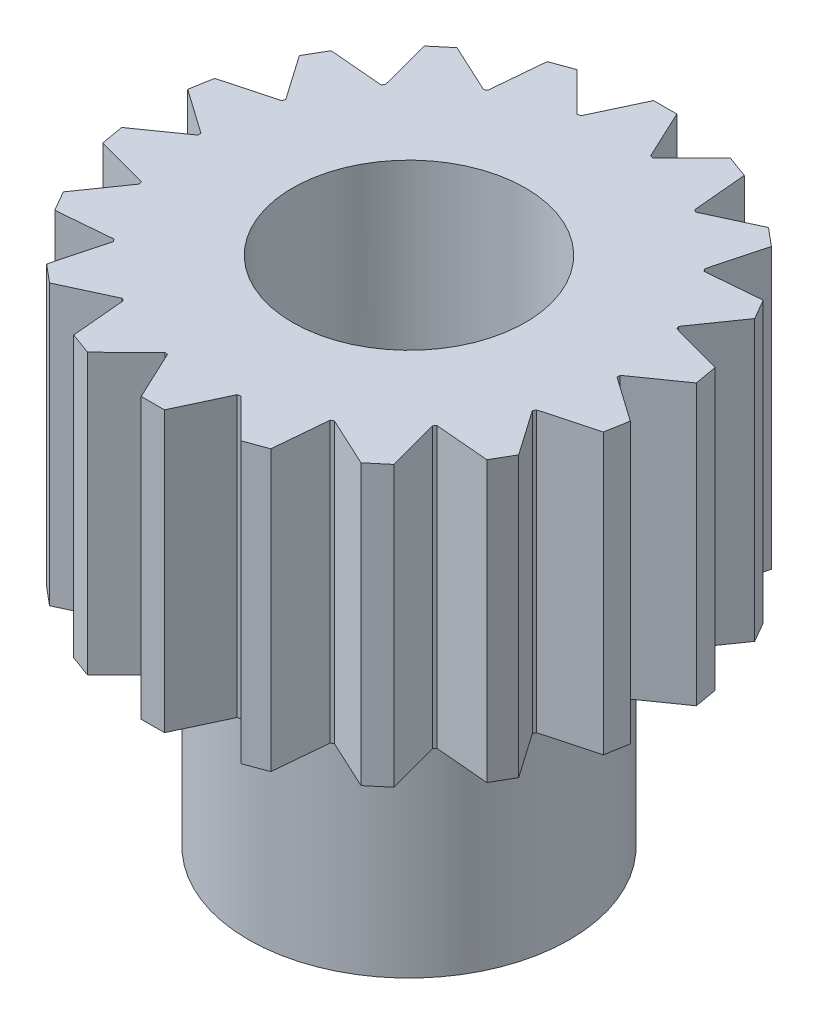
SolidWorks part; units mm, degrees
material "PE High Density Film"
ref_plane "Front Plane" through (0, 0, 0) normal (0, 0, 1) x (1, 0, 0)
ref_plane "Top Plane" through (0, 0, 0) normal (0, 1, 0) x (1, 0, 0)
ref_plane "Right Plane" through (0, 0, 0) normal (1, 0, 0) x (0, 0, -1)
sketch "Sketch1" plane through (0, 0, 0) normal (0, 1, 0) x (1, 0, 0)
  line L0 (0, 2.285) -> (0, -2.285) construction
  circle A0 centre (0, 0) radius 1.27
  circle A1 centre (0, 0) radius 2.285
  dimension "D1" = 2.54
  dimension "D2" = 4.57
extrude "Boss-Extrude1" add sketch "Sketch1" along normal blind 3.048
ref_plane "Plane1" through (0, 3.048, 0) normal (0, 1, 0) x (1, 0, 0)
sketch "Sketch2" plane through (0, 3.048, 0) normal (0, 1, 0) x (1, 0, 0)
  line L0 (0, 2.285) -> (0, -2.285) construction
  line L4 (-0.127, 2.7929) -> (0.127, 2.7929)
  line L5 (-0.127, 2.7929) -> (-0.38, 2.2531)
  line L6 (0.127, 2.7929) -> (0.38, 2.2531)
  circle A0 centre (0, 0) radius 2.285 construction
  arc A2 (0.38, 2.2531) -> (-0.38, 2.2531) centre (0, 0.0029) ccw
  point P12 (0, 2.285)
  point P14 (0, 2.285)
  dimension "D3" = 0.76
  dimension "D1" = 0.254
  dimension "D2" = 2.79
extrude "Boss-Extrude2" add sketch "Sketch2" against normal blind 3.048
pattern_circular "CirPattern1" count 18 over 360 about axis through (0, 0, 0) along (0, 1, 0) of "Boss-Extrude2"
sketch "Sketch3" plane through (0, 0, 0) normal (0, -1, 0) x (1, 0, 0)
  circle A0 centre (0, 0) radius 1.27
  circle A1 centre (0, 0) radius 1.75
  dimension "D1" = 3.5
  dimension "D2" = 2.54
extrude "Boss-Extrude3" add sketch "Sketch3" along normal blind 2.54
